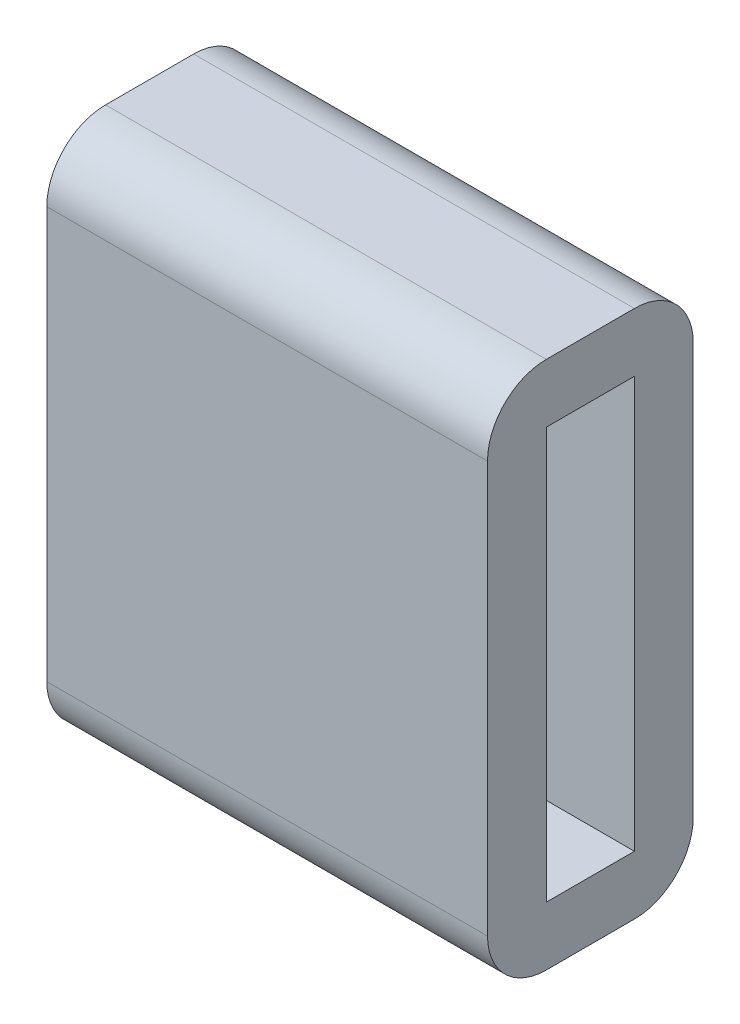
SolidWorks part; units mm, degrees
ref_plane "Přední rovina" through (0, 0, 0) normal (0, 0, 1) x (1, 0, 0)
ref_plane "Horní rovina" through (0, 0, 0) normal (0, 1, 0) x (1, 0, 0)
ref_plane "Pravá rovina" through (0, 0, 0) normal (1, 0, 0) x (0, 0, -1)
sketch "Skica1" plane through (0, 0, 0) normal (0, 0, 1) x (1, 0, 0)
  line L1 (-3.75, 4.5) -> (3.75, 4.5)
  line L2 (-3.75, 4.5) -> (-3.75, -4.5)
  line L3 (-3.75, -4.5) -> (3.75, -4.5)
  line L4 (3.75, 4.5) -> (3.75, -4.5)
  line L5 (-3.75, 4.5) -> (3.75, -4.5) construction
  line L6 (-3.75, -4.5) -> (3.75, 4.5) construction
  point P0 (0, 0)
  dimension "D1" = 9
  dimension "D2" = 7.5
extrude "Přidat vysunutím1" add sketch "Skica1" along normal blind 3.5
fillet "Zaoblit1" radius 1 4 edges at (0, -4.5, 3.5) (0, 4.5, 3.5) (0, -4.5, 0) (0, 4.5, 0)
sketch "Skica2" plane through (3.75, 0, 0) normal (1, 0, 0) x (0, 0, -1)
  line L0 (0, -3.5) -> (0, 3.5) construction
  line L1 (-2.5, 3.5) -> (-1, 3.5)
  line L2 (-2.5, 3.5) -> (-2.5, -3.5)
  line L3 (-2.5, -3.5) -> (-1, -3.5)
  line L4 (-1, 3.5) -> (-1, -3.5)
  line L5 (-2.5, 3.5) -> (-1, -3.5) construction
  line L6 (-2.5, -3.5) -> (-1, 3.5) construction
  line L8 (-2.5, -4.5) -> (-1, -4.5) construction
  point P0 (-1.75, 0)
  dimension "D1" = 1.75
  dimension "D2" = 4.5
  dimension "D3" = 1.5
  dimension "D4" = 7
extrude "Odebrat vysunutím1" cut sketch "Skica2" against normal blind 5 contours L4 L3 L2 L1
